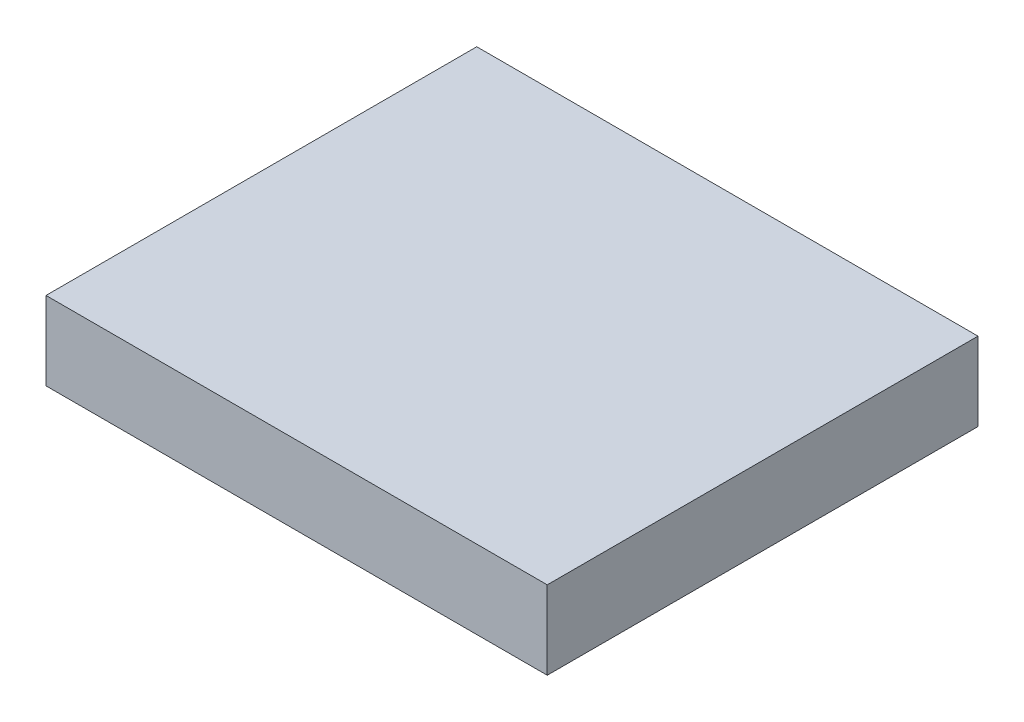
SolidWorks part; units mm, degrees
ref_plane "Front Plane" through (0, 0, 0) normal (0, 0, 1) x (1, 0, 0)
ref_plane "Top Plane" through (0, 0, 0) normal (0, 1, 0) x (1, 0, 0)
ref_plane "Right Plane" through (0, 0, 0) normal (1, 0, 0) x (0, 0, -1)
sketch "Sketch1" plane through (0, 0, 0) normal (0, 1, 0) x (1, 0, 0)
  line L1 (-406.4, 349.25) -> (406.4, 349.25)
  line L2 (-406.4, 349.25) -> (-406.4, -349.25)
  line L3 (-406.4, -349.25) -> (406.4, -349.25)
  line L4 (406.4, 349.25) -> (406.4, -349.25)
  line L5 (-406.4, 349.25) -> (406.4, -349.25) construction
  line L6 (-406.4, -349.25) -> (406.4, 349.25) construction
  point P0 (0, 0)
  dimension "D1" = 698.5
  dimension "D2" = 812.8
extrude "Boss-Extrude1" add sketch "Sketch1" along normal blind 127
